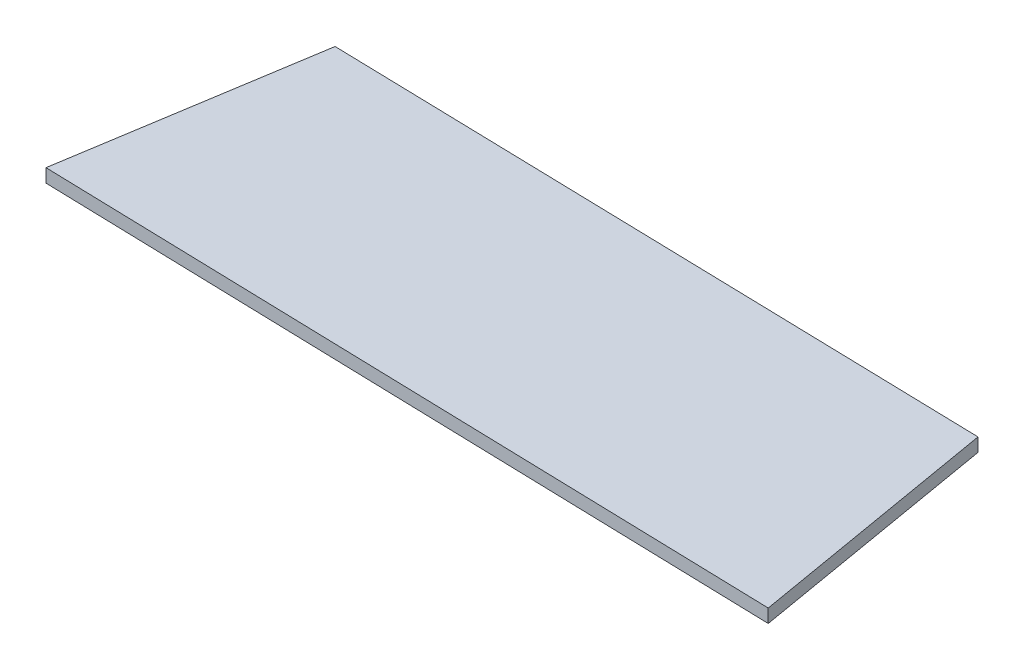
SolidWorks part; units mm, degrees
ref_plane "Plan de face" through (0, 0, 0) normal (0, 0, 1) x (1, 0, 0)
ref_plane "Plan de dessus" through (0, 0, 0) normal (0, 1, 0) x (1, 0, 0)
ref_plane "Plan de droite" through (0, 0, 0) normal (1, 0, 0) x (0, 0, -1)
sketch "Esquisse1" plane through (0, 0, 0) normal (0, 1, 0) x (1, 0, 0)
  line L0 (5.9103, 37.2021) -> (0, 0)
  line L1 (0, 0) -> (110.7174, -3.0207)
  line L2 (110.7174, -3.0207) -> (104.2607, 34.7154)
  line L3 (104.2607, 34.7154) -> (5.9103, 37.2021)
  point P4 (0, 0)
extrude "Boss.-Extru.1" add sketch "Esquisse1" along normal blind 2
